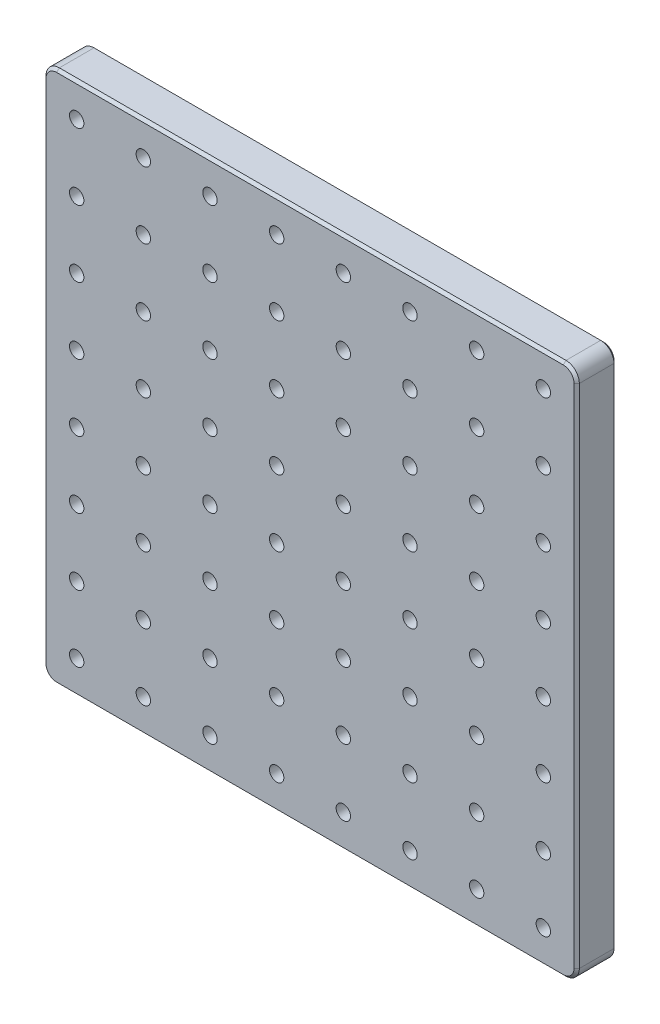
SolidWorks part; units mm, degrees
ref_plane "Front Plane" through (0, 0, 0) normal (0, 0, 1) x (1, 0, 0)
ref_plane "Top Plane" through (0, 0, 0) normal (0, 1, 0) x (1, 0, 0)
ref_plane "Right Plane" through (0, 0, 0) normal (1, 0, 0) x (0, 0, -1)
sketch "Sketch1" plane through (0, 0, 0) normal (0, 0, 1) x (1, 0, 0)
  line L1 (-200, 200) -> (200, 200)
  line L2 (-200, 200) -> (-200, -200)
  line L3 (-200, -200) -> (200, -200)
  line L4 (200, 200) -> (200, -200)
  line L5 (-200, 200) -> (200, -200) construction
  line L6 (-200, -200) -> (200, 200) construction
  point P0 (0, 0)
  dimension "D1" = 400
  dimension "D2" = 400
extrude "Boss-Extrude1" add sketch "Sketch1" along normal mid plane 30
hole_wizard "M12x1.25 Tapped Hole1" positions "Sketch3" profile "Sketch2" tap size "M12x1.25" standard "ISO"
sketch "Sketch3" plane through (0, 0, 15) normal (0, 0, 1) x (1, 0, 0)
  line L0 (200, 200) -> (-200, 200) construction
  line L1 (-200, 200) -> (-200, -200) construction
  point P0 (-175, 175)
  dimension "D1" = 25
  dimension "D2" = 25
sketch "Sketch2" plane through (-175, 175, 15) normal (1, 0, 0) x (0, -1, 0)
  line L0 (0, 0) -> (0, 33.2446)
  line L1 (0, 33.2446) -> (5.4, 30)
  line L2 (5.4, 30) -> (5.4, 0)
  line L5 (5.4, 0) -> (0, 0)
  line L10 (0, 33.2446) -> (-5.4, 30) construction
  line L11 (0, -6.35) -> (0, 107.95) construction
  dimension "Tap Drill Dia." = 10.8
  dimension "Tap Drill Depth" = 30
  dimension "Drill Angle" = 118
cosmetic thread "Hole Thread1" parameters "D1"=30, "D2"=12
pattern_linear "LPattern1" count 8 spacing 50 along (1, 0, 0) count 8 spacing 50 along (0, -1, 0) of "M12x1.25 Tapped Hole1"
fillet "Fillet1" radius 10 4 edges at (200, -200, 0) (200, 200, 0) (-200, 200, 0) (-200, -200, 0)
chamfer "Chamfer1" distance 2 angle 45 8 edges at (-197.0711, -197.0711, 15) (0, -200, 15) (197.0711, -197.0711, 15) (200, 0, 15) (197.0711, 197.0711, 15) (-200, 0, 15) (-197.0711, 197.0711, 15) (0, 200, 15)
chamfer "Chamfer2" distance 2 angle 45 8 edges at (197.0711, 197.0711, -15) (200, 0, -15) (197.0711, -197.0711, -15) (0, -200, -15) (-197.0711, -197.0711, -15) (0, 200, -15) (-200, 0, -15) (-197.0711, 197.0711, -15)
